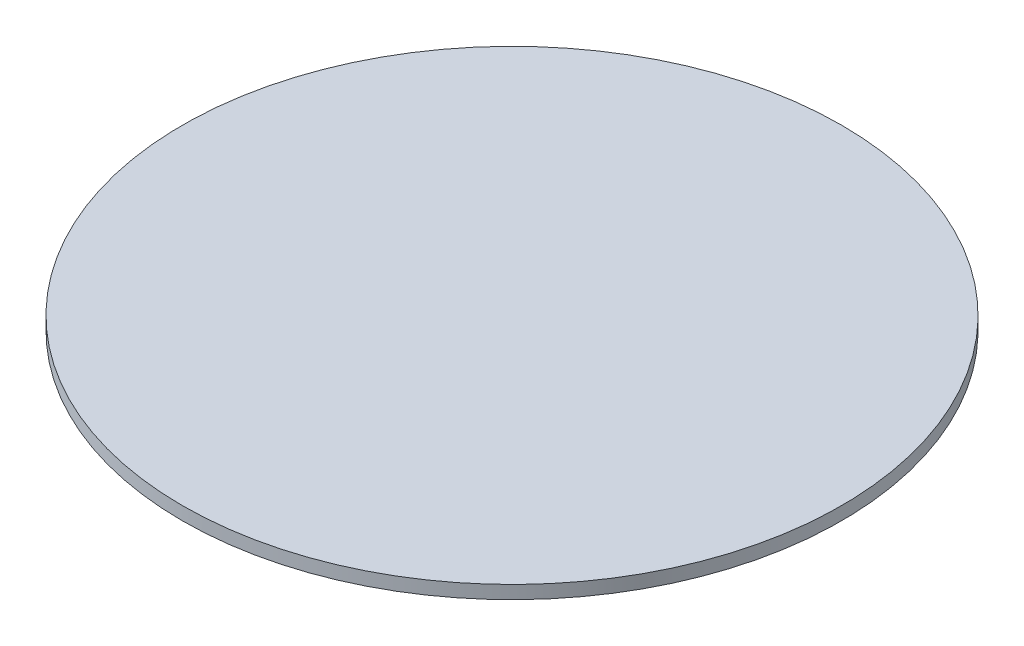
SolidWorks part; units mm, degrees
ref_plane "Plano frontal" through (0, 0, 0) normal (0, 0, 1) x (1, 0, 0)
ref_plane "Plano superior" through (0, 0, 0) normal (0, 1, 0) x (1, 0, 0)
ref_plane "Plano direito" through (0, 0, 0) normal (1, 0, 0) x (0, 0, -1)
sketch "Esboço1" plane through (0, 0, 0) normal (0, 1, 0) x (1, 0, 0)
  circle A0 centre (0, 0) radius 1000
  dimension "D1" = 2000
extrude "Ressalto-extrusão1" add sketch "Esboço1" along normal blind 40
